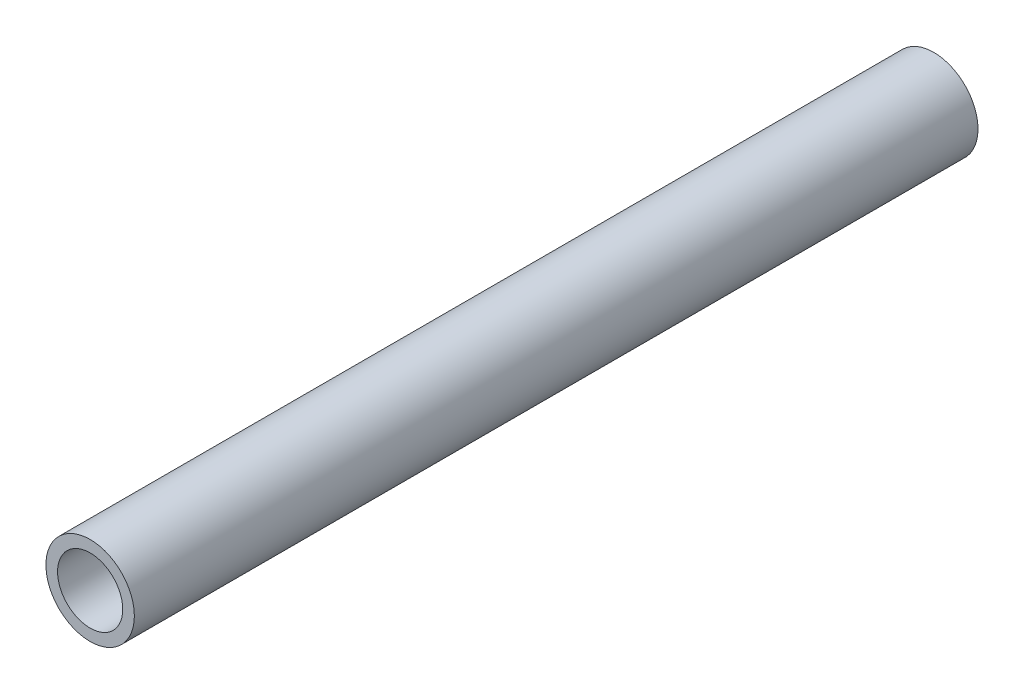
SolidWorks part; units mm, degrees
ref_plane "Front Plane" through (0, 0, 0) normal (0, 0, 1) x (1, 0, 0)
ref_plane "Top Plane" through (0, 0, 0) normal (0, 1, 0) x (1, 0, 0)
ref_plane "Right Plane" through (0, 0, 0) normal (1, 0, 0) x (0, 0, -1)
sketch "Sketch1" plane through (0, 0, 0) normal (0, 0, 1) x (1, 0, 0)
  circle A0 centre (0, 0) radius 4.826
  circle A1 centre (0, 0) radius 3.556
  dimension "D1" = 7.112
  dimension "D2" = 1.27
extrude "Boss-Extrude1" add sketch "Sketch1" along normal blind 92.075
